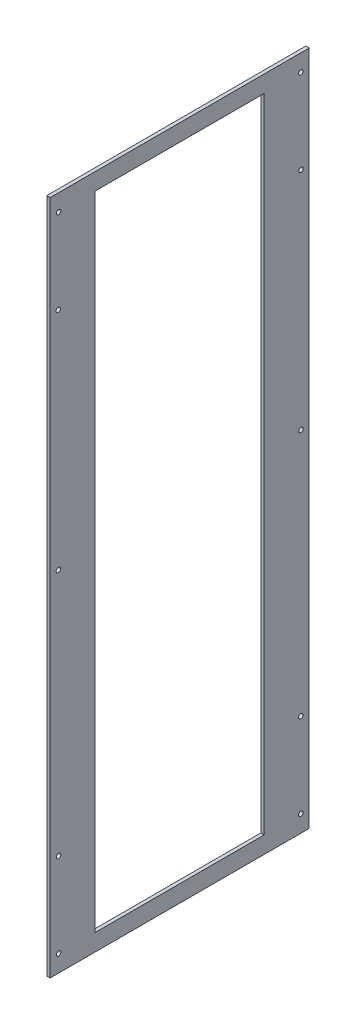
SolidWorks part; units mm, degrees
ref_plane "前视基准面" through (0, 0, 0) normal (0, 0, 1) x (1, 0, 0)
ref_plane "上视基准面" through (0, 0, 0) normal (0, 1, 0) x (1, 0, 0)
ref_plane "右视基准面" through (0, 0, 0) normal (1, 0, 0) x (0, 0, -1)
other "Configuration Table"
sketch "草图1" plane through (0, 0, 0) normal (1, 0, 0) x (0, 0, -1)
  line L0 (-115, 0) -> (115, 0) construction
  line L1 (-115, -300) -> (115, -300)
  line L2 (-115, -300) -> (-115, 300)
  line L3 (-115, 300) -> (115, 300)
  line L4 (115, -300) -> (115, 300)
  line L5 (-115, -300) -> (115, 300) construction
  line L6 (-115, 300) -> (115, -300) construction
  line L7 (-75, -285) -> (75, -285)
  line L8 (-75, -285) -> (-75, 285)
  line L9 (-75, 285) -> (75, 285)
  line L10 (75, -285) -> (75, 285)
  line L11 (-75, -285) -> (75, 285) construction
  line L12 (-75, 285) -> (75, -285) construction
  line L13 (0, -300) -> (0, 300) construction
  circle A0 centre (-107.5, 285) radius 2
  circle A1 centre (-107.698, 210) radius 2
  circle A2 centre (-107.5, -210) radius 2
  circle A3 centre (-107.5, -285) radius 2
  circle A4 centre (-107.698, 10) radius 2
  circle A5 centre (107.5, -285) radius 2
  circle A6 centre (107.5, -210) radius 2
  circle A7 centre (107.698, 210) radius 2
  circle A8 centre (107.5, 285) radius 2
  circle A9 centre (107.698, 10) radius 2
  point P0 (0, 0)
  point P6 (0, 0)
  point P14 (0, 0)
  point P18 (0, 0)
  dimension "D6" = 4
  dimension "D9" = 4
  dimension "D11" = 4
  dimension "D15" = 4
  dimension "D16" = 4
  dimension "D1" = 600
  dimension "D2" = 230
  dimension "D3" = 570
  dimension "D4" = 150
  dimension "D5" = 15
  dimension "D7" = 7.5
  dimension "D8" = 90
  dimension "D10" = 15
  dimension "D12" = 7.5
  dimension "D13" = 7.5
  dimension "D14" = 90
  dimension "D17" = 290
extrude "凸台-拉伸1" add sketch "草图1" along normal blind 3
